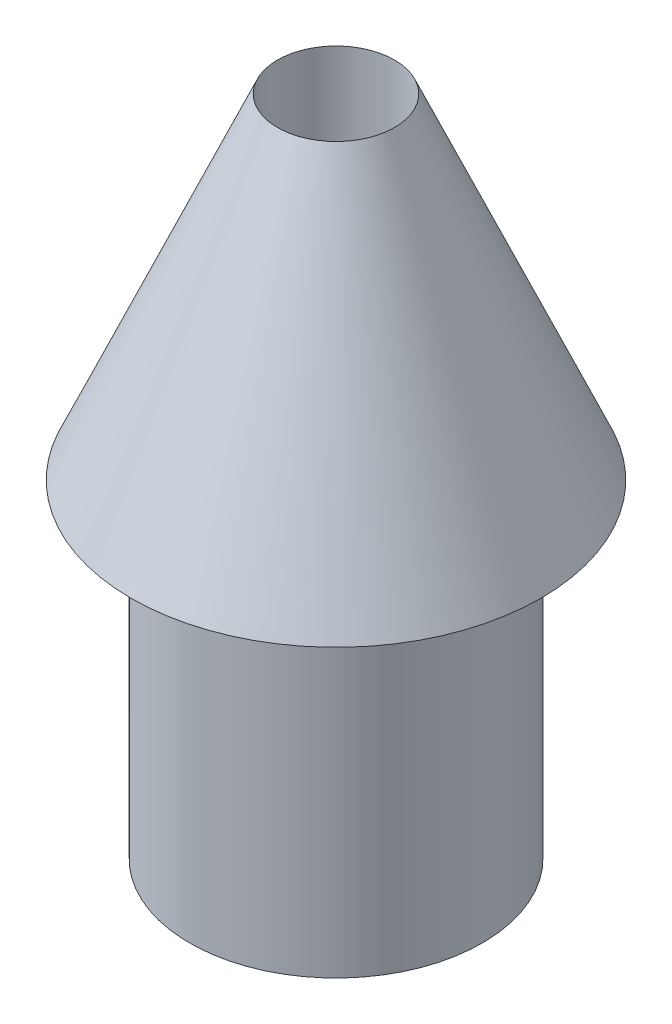
SolidWorks part; units mm, degrees
ref_plane "Plan de face" through (0, 0, 0) normal (0, 0, 1) x (1, 0, 0)
ref_plane "Plan de dessus" through (0, 0, 0) normal (0, 1, 0) x (1, 0, 0)
ref_plane "Plan de droite" through (0, 0, 0) normal (1, 0, 0) x (0, 0, -1)
sketch "Esquisse1" plane through (0, 0, 0) normal (0, 0, 1) x (1, 0, 0)
  line L0 (0, 0) -> (1.75, 0)
  line L1 (0, 0) -> (0, 4)
  line L2 (0, 4) -> (1.75, 0)
  dimension "D1" = 1.75
  dimension "D2" = 4
revolve "Révolution1" add sketch "Esquisse1" angle 360 about L1
sketch "Esquisse3" plane through (0, 0, 0) normal (0, -1, 0) x (-1, 0, 0)
  circle A0 centre (0, 0) radius 1.25
  dimension "D1" = 2.5
extrude "Boss.-Extru.1" add sketch "Esquisse3" along normal blind 2.8
sketch "Esquisse4" plane through (0, -2.8, 0) normal (0, -1, 0) x (1, 0, 0)
  circle A0 centre (0, 0) radius 0.5
  dimension "D1" = 1
extrude "Enlèv. mat.-Extru.1" cut sketch "Esquisse4" against normal blind 13
